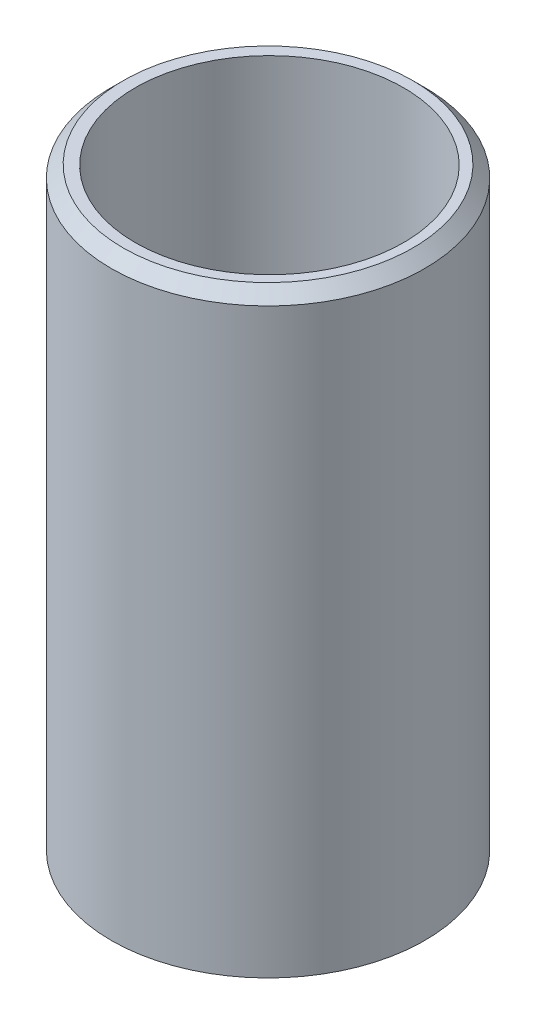
SolidWorks part; units mm, degrees
ref_plane "Front Plane" through (0, 0, 0) normal (0, 0, 1) x (1, 0, 0)
ref_plane "Top Plane" through (0, 0, 0) normal (0, 1, 0) x (1, 0, 0)
ref_plane "Right Plane" through (0, 0, 0) normal (1, 0, 0) x (0, 0, -1)
sketch "Sketch1" plane through (0, 0, 0) normal (0, 1, 0) x (1, 0, 0)
  circle A0 centre (-13.4146, 13.2881) radius 16.764
extrude "Boss-Extrude1" add sketch "Sketch1" along normal blind 63.5 contours A0
sketch "Sketch2" plane through (0, 0, 0) normal (0, 1, 0) x (1, 0, 0)
  line L0 (-12.1811, 30.0066) -> (-14.336, -3.4506) construction
  circle A0 centre (-13.4146, 13.2881) radius 16.764 construction
  circle A1 centre (-13.2586, 13.278) radius 14.351
  point P6 (0, 0)
  point P7 (-15.2574, -20.1892)
extrude "Cut-Extrude1" cut sketch "Sketch2" along normal blind 166.37
chamfer "Chamfer1" distance 1.27 angle 45 1 edges at (-13.4146, 63.5, 3.4759)
